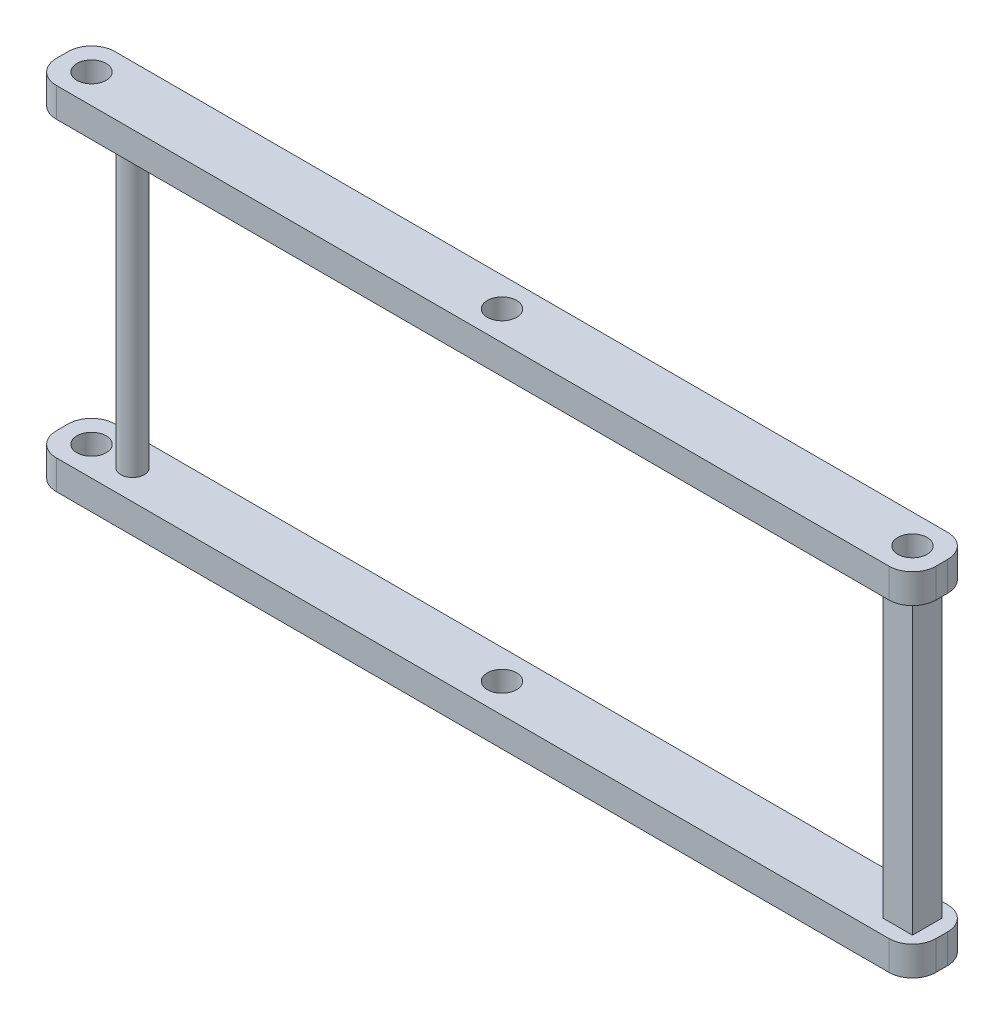
SolidWorks part; units mm, degrees
ref_plane "Alzado" through (0, 0, 0) normal (0, 0, 1) x (1, 0, 0)
ref_plane "Planta" through (0, 0, 0) normal (0, 1, 0) x (1, 0, 0)
ref_plane "Vista lateral" through (0, 0, 0) normal (1, 0, 0) x (0, 0, -1)
sketch "Croquis1" plane through (0, 0, 0) normal (0, 1, 0) x (1, 0, 0)
  line L0 (0, 5) -> (0, -5) construction
  line L1 (-75, -5) -> (75, -5)
  line L2 (-75, -5) -> (-75, 5)
  line L3 (-75, 5) -> (75, 5)
  line L4 (75, -5) -> (75, 5)
  line L5 (-75, -5) -> (75, 5) construction
  line L6 (-75, 5) -> (75, -5) construction
  circle A0 centre (-70, 0) radius 2.5
  circle A1 centre (70, 0) radius 2.5
  circle A2 centre (0, 0) radius 2.5
  point P0 (0, 0)
  dimension "D3" = 5
  dimension "D5" = 5
  dimension "D1" = 150
  dimension "D2" = 10
  dimension "D4" = 5
  dimension "D6" = 5
extrude "Saliente-Extruir1" add sketch "Croquis1" along normal blind 5
fillet "Redondeo1" radius 4 4 edges at (75, 2.5, 5) (75, 2.5, -5) (-75, 2.5, -5) (-75, 2.5, 5)
sketch "Croquis2" plane through (0, 5, 0) normal (0, 1, 0) x (1, 0, 0)
  line L1 (67.5, -2.5) -> (72.5, -2.5)
  line L2 (67.5, -2.5) -> (67.5, 2.5)
  line L3 (67.5, 2.5) -> (72.5, 2.5)
  line L4 (72.5, -2.5) -> (72.5, 2.5)
  line L5 (67.5, -2.5) -> (72.5, 2.5) construction
  line L6 (67.5, 2.5) -> (72.5, -2.5) construction
  circle A0 centre (-63, 0) radius 2
  circle A1 centre (-70, 0) radius 2.5 construction
  point P4 (70, 0)
  dimension "D1" = 4
  dimension "D2" = 7
  dimension "D3" = 5
  dimension "D4" = 5
extrude "Saliente-Extruir2" add sketch "Croquis2" along normal blind 50 and the other way blind 0.01 contours A0 | L2 L1 L4 L3
sketch "Croquis3" plane through (0, 55, 0) normal (0, 1, 0) x (1, 0, 0)
  line L0 (-75, 1) -> (-75, -1) construction
  line L1 (-75, 1) -> (-75, -1)
  line L2 (75, -1) -> (75, 1) construction
  line L3 (-71, -5) -> (71, -5) construction
  line L4 (71, 5) -> (-71, 5) construction
  line L5 (75, -1) -> (75, 1)
  line L6 (-71, -5) -> (71, -5)
  line L7 (71, 5) -> (-71, 5)
  circle A0 centre (70, 0) radius 2.5 construction
  arc A3 (71, -5) -> (75, -1) centre (71, -1) ccw construction
  arc A4 (75, 1) -> (71, 5) centre (71, 1) ccw construction
  circle A5 centre (0, 0) radius 2.5 construction
  circle A6 centre (-70, 0) radius 2.5 construction
  arc A7 (-71, 5) -> (-75, 1) centre (-71, 1) ccw construction
  arc A8 (-75, -1) -> (-71, -5) centre (-71, -1) ccw construction
  circle A9 centre (70, 0) radius 2.5
  arc A10 (71, -5) -> (75, -1) centre (71, -1) ccw
  arc A11 (75, 1) -> (71, 5) centre (71, 1) ccw
  circle A12 centre (0, 0) radius 2.5
  circle A13 centre (-70, 0) radius 2.5
  arc A14 (-71, 5) -> (-75, 1) centre (-71, 1) ccw
  arc A15 (-75, -1) -> (-71, -5) centre (-71, -1) ccw
extrude "Saliente-Extruir10" add sketch "Croquis3" along normal blind 5 and the other way blind 0.001 contours A13 | L1 A15 L6 A10 L5 A11 L7 A14 | A9 | A12
